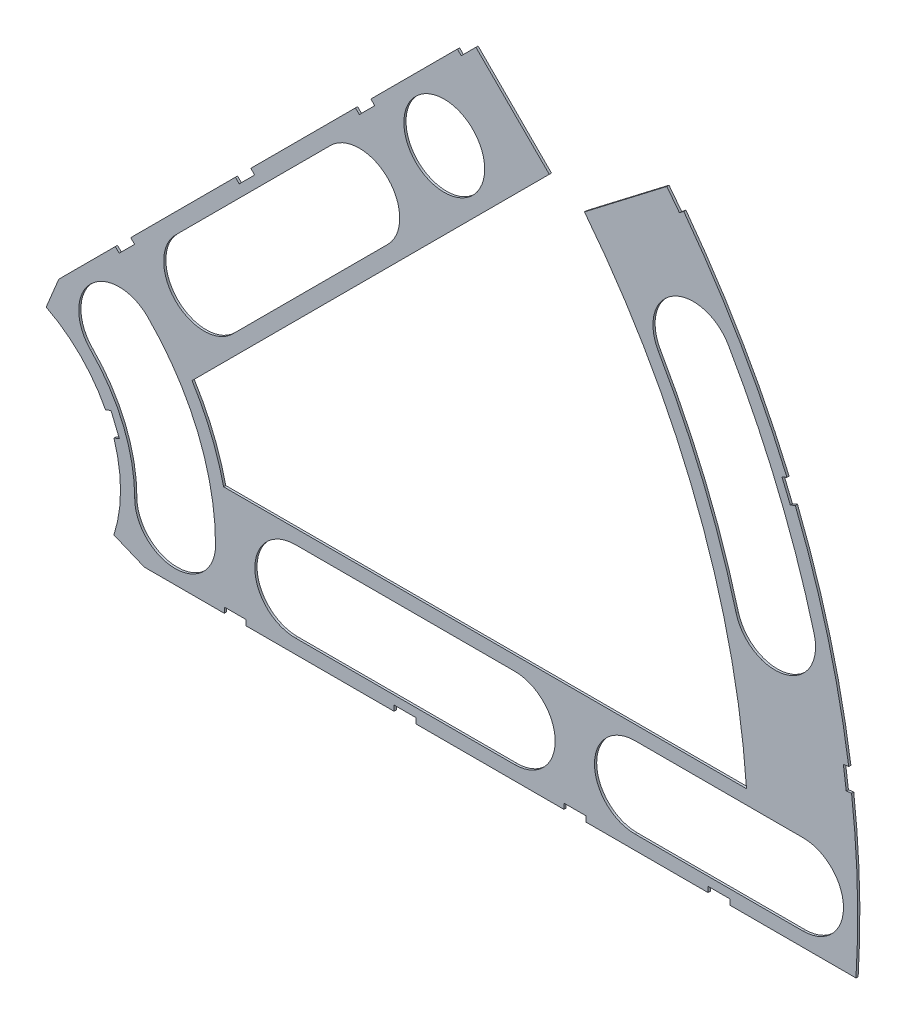
SolidWorks part; units mm, degrees
material "PTFE (general)"
ref_plane "Front Plane" through (0, 0, 0) normal (0, 0, 1) x (1, 0, 0)
ref_plane "Top Plane" through (0, 0, 0) normal (0, 1, 0) x (1, 0, 0)
ref_plane "Right Plane" through (0, 0, 0) normal (1, 0, 0) x (0, 0, -1)
sketch "Sketch1" plane through (0, 0, 0) normal (0, 0, 1) x (1, 0, 0)
  line L0 (0, 0) -> (320.3893, 0) construction
  line L1 (0, 0) -> (155.5285, 155.5285) construction
  line L2 (67.2115, 76.1917) -> (8.6967, 17.6769)
  line L3 (8.6967, 17.6769) -> (7.229, 14.1336)
  line L4 (101.4014, -6.35) -> (18.6489, -6.35)
  line L5 (15.1056, -4.8823) -> (18.6489, -6.35)
  line L6 (88.6729, 6.35) -> (27.8605, 6.35)
  line L9 (67.1914, 58.2111) -> (24.1905, 15.2102)
  line L10 (0, 0) -> (40.4486, 97.6516) construction
  line L11 (0, 0) -> (123.4567, -51.1374) construction
  line L18 (8.6967, 17.6769) -> (13.294, 8.6183) construction
  line L19 (18.6489, -6.35) -> (15.4943, 3.3063) construction
  line L20 (27.8605, 6.35) -> (27.7442, 6.7059) construction
  line L21 (24.1905, 15.2102) -> (24.3599, 14.8764) construction
  arc A0 (7.229, 14.1336) -> (15.1056, -4.8823) centre (0, 0) cw
  arc A1 (67.2115, 76.1917) -> (101.4014, -6.35) centre (0, 0) cw
  arc A2 (24.1905, 15.2102) -> (27.8605, 6.35) centre (0, 0) cw
  arc A3 (67.1914, 58.2111) -> (88.6729, 6.35) centre (0, 0) cw
  arc A8 (13.294, 8.6183) -> (15.4943, 3.3063) centre (0, 0) cw construction
  arc A9 (24.3599, 14.8764) -> (27.7442, 6.7059) centre (0, 0) cw construction
  dimension "D1" = 45
  dimension "D3" = 6.35
  dimension "D4" = 15.875
  dimension "D7" = 22.5
  dimension "D8" = 101.6
  dimension "D11" = 12.7
  dimension "D12" = 12.7
  dimension "D2" = 6.35
  dimension "D5" = 67.5
  dimension "D9" = 1.27
  dimension "D10" = 1.27
  dimension "D6" = 12.7
extrude "Boss-Extrude1" add sketch "Sketch1" along normal blind 0.254
sketch "Sketch2" plane through (0, 0, 0.254) normal (0, 0, 1) x (1, 0, 0)
  line L0 (0, 0) -> (101.6, 0) construction
  line L1 (0, 0) -> (71.842, 71.842) construction
  line L3 (0, 0) -> (22.225, 0) construction
  line L4 (0, 0) -> (15.7154, 15.7154) construction
  line L5 (0, 0) -> (95.25, 0) construction
  line L6 (0, 0) -> (92.0044, 24.6525) construction
  arc A0 (101.4014, -6.35) -> (67.2115, 76.1917) centre (0, 0) ccw construction
  circle A1 centre (22.225, 0) radius 4.699
  arc A2 (15.1056, -4.8823) -> (7.229, 14.1336) centre (0, 0) ccw construction
  circle A3 centre (36.195, 0) radius 4.699
  circle A4 centre (61.722, 0) radius 4.699
  circle A5 centre (75.692, 0) radius 4.699
  circle A6 centre (95.25, 0) radius 4.699
  circle A7 centre (15.7154, 15.7154) radius 4.699
  circle A8 centre (25.5937, 25.5937) radius 4.699
  circle A9 centre (43.644, 43.644) radius 4.699
  circle A10 centre (53.5223, 53.5223) radius 4.699
  circle A11 centre (92.0044, 24.6525) radius 4.699
  circle A12 centre (82.4889, 47.625) radius 4.699
  circle A13 centre (67.3519, 67.3519) radius 4.699
  dimension "D3" = 9.398
  dimension "D1" = 45
  dimension "D2" = 6.35
  dimension "D4" = 6.35
  dimension "D5" = 13.97
  dimension "D7" = 13.97
  dimension "D8" = 19.558
  dimension "D9" = 45
  dimension "D10" = 15
  dimension "D11" = 25.527
  dimension "D6" = 2
extrude "Cut-Extrude1" cut sketch "Sketch2" against normal through all
sketch "Sketch3" plane through (0, 0, 0.254) normal (0, 0, 1) x (1, 0, 0)
  line L0 (15.2664, 24.2467) -> (17.0625, 26.0427)
  line L1 (15.2664, 24.2467) -> (15.7154, 23.7977)
  line L2 (17.0625, 26.0427) -> (17.5115, 25.5937)
  line L3 (15.7154, 23.7977) -> (17.5115, 25.5937)
  line L4 (67.2115, 76.1917) -> (8.6967, 17.6769) construction
  line L5 (44.9911, 53.9713) -> (43.195, 52.1753)
  line L6 (44.9911, 53.9713) -> (45.4401, 53.5223)
  line L7 (43.195, 52.1753) -> (43.644, 51.7263)
  line L8 (45.4401, 53.5223) -> (43.644, 51.7263)
  line L9 (27.94, -6.35) -> (30.48, -6.35)
  line L10 (27.94, -6.35) -> (27.94, -5.715)
  line L11 (30.48, -6.35) -> (30.48, -5.715)
  line L12 (27.94, -5.715) -> (30.48, -5.715)
  line L13 (18.6489, -6.35) -> (101.4014, -6.35) construction
  line L14 (67.437, -6.35) -> (69.977, -6.35)
  line L15 (67.437, -6.35) -> (67.437, -5.715)
  line L16 (69.977, -6.35) -> (69.977, -5.715)
  line L17 (67.437, -5.715) -> (69.977, -5.715)
  line L18 (29.2307, 38.211) -> (31.0268, 40.007)
  line L19 (29.2307, 38.211) -> (29.6797, 37.762)
  line L20 (31.0268, 40.007) -> (31.4758, 39.558)
  line L21 (29.6797, 37.762) -> (31.4758, 39.558)
  line L22 (56.845, 65.8253) -> (55.049, 64.0292)
  line L23 (56.845, 65.8253) -> (57.294, 65.3763)
  line L24 (55.049, 64.0292) -> (55.498, 63.5802)
  line L25 (57.294, 65.3763) -> (55.498, 63.5802)
  line L26 (47.6885, -6.35) -> (50.2285, -6.35)
  line L27 (47.6885, -6.35) -> (47.6885, -5.715)
  line L28 (50.2285, -6.35) -> (50.2285, -5.715)
  line L29 (47.6885, -5.715) -> (50.2285, -5.715)
  line L30 (84.201, -6.35) -> (86.741, -6.35)
  line L31 (84.201, -6.35) -> (84.201, -5.715)
  line L32 (86.741, -6.35) -> (86.741, -5.715)
  line L33 (84.201, -5.715) -> (86.741, -5.715)
  line L34 (0, 0) -> (100.7308, 13.2615) construction
  line L35 (0, 0) -> (93.8662, 38.8806) construction
  line L36 (0, 0) -> (80.6047, 61.8502) construction
  line L37 (0, 0) -> (101.6, 0) construction
  line L38 (99.9355, 14.4377) -> (100.267, 11.9194)
  line L39 (99.9355, 14.4377) -> (101.1946, 14.6035)
  line L40 (100.267, 11.9194) -> (101.5261, 12.0852)
  line L41 (101.1946, 14.6035) -> (101.5261, 12.0852)
  line L42 (99.9355, 14.4377) -> (101.5261, 12.0852) construction
  line L43 (100.267, 11.9194) -> (101.1946, 14.6035) construction
  line L44 (93.7655, 37.4643) -> (94.9388, 37.9503)
  line L45 (93.7655, 37.4643) -> (92.7935, 39.811)
  line L46 (94.9388, 37.9503) -> (93.9668, 40.297)
  line L47 (92.7935, 39.811) -> (93.9668, 40.297)
  line L48 (93.7655, 37.4643) -> (93.9668, 40.297) construction
  line L49 (94.9388, 37.9503) -> (92.7935, 39.811) construction
  line L50 (79.3278, 62.4712) -> (80.874, 60.456)
  line L51 (79.3278, 62.4712) -> (80.3354, 63.2443)
  line L52 (80.874, 60.456) -> (81.8816, 61.2292)
  line L53 (80.3354, 63.2443) -> (81.8816, 61.2292)
  line L54 (79.3278, 62.4712) -> (81.8816, 61.2292) construction
  line L55 (80.874, 60.456) -> (80.3354, 63.2443) construction
  line L56 (13.5939, 7.0054) -> (14.5659, 4.6588)
  line L57 (13.5939, 7.0054) -> (14.7672, 7.4914)
  line L58 (14.5659, 4.6588) -> (15.7393, 5.1448)
  line L59 (14.7672, 7.4914) -> (15.7393, 5.1448)
  line L60 (13.5939, 7.0054) -> (15.7393, 5.1448) construction
  line L61 (14.5659, 4.6588) -> (14.7672, 7.4914) construction
  circle A0 centre (15.7154, 15.7154) radius 4.699 construction
  circle A1 centre (43.644, 43.644) radius 4.699 construction
  circle A2 centre (22.225, 0) radius 4.699 construction
  circle A3 centre (61.722, 0) radius 4.699 construction
  arc A4 (101.4014, -6.35) -> (67.2115, 76.1917) centre (0, 0) ccw construction
  arc A9 (15.1056, -4.8823) -> (7.229, 14.1336) centre (0, 0) ccw construction
  circle A10 centre (36.195, 0) radius 4.699 construction
  circle A11 centre (75.692, 0) radius 4.699 construction
  circle A12 centre (25.5937, 25.5937) radius 4.699 construction
  circle A13 centre (53.5223, 53.5223) radius 4.699 construction
  point P75 (14.6666, 6.0751)
  dimension "D2" = 5.715
  dimension "D3" = 2.54
  dimension "D6" = 5.715
  dimension "D8" = 0.635
  dimension "D9" = 5.715
  dimension "D12" = 5.715
  dimension "D4" = 7.5
  dimension "D5" = 22.5
  dimension "D7" = 37.5
  dimension "D10" = 90
  dimension "D11" = 1.27
  dimension "D14" = 0.635
  dimension "D15" = 90
  dimension "D18" = 0.635
  dimension "D19" = 90
  dimension "D22" = 0.635
  dimension "D20" = 1.27
  dimension "D17" = 0.635
  dimension "D13" = 11.4935
  dimension "D16" = 8.509
  dimension "D21" = 11.4935
  dimension "D23" = 8.509
extrude "Cut-Extrude2" cut sketch "Sketch3" against normal through all
sketch "Sketch5" plane through (0, 0, 0.254) normal (0, 0, 1) x (1, 0, 0)
  line L0 (0, 0) -> (85.5465, 65.6421) construction
  line L1 (55.8572, 66.6335) -> (68.4933, 53.9974)
  line L2 (68.4933, 53.9974) -> (81.5013, 63.9789)
  line L3 (67.3519, 78.1282) -> (81.5013, 63.9789)
  line L5 (67.3519, 78.1282) -> (55.8572, 66.6335)
  line L8 (69.977, -6.35) -> (84.201, -6.35) construction
  line L9 (55.049, 64.0292) -> (55.498, 63.5802) construction
  line L10 (67.2115, 76.1917) -> (56.845, 65.8253) construction
  arc A1 (79.8253, 62.8529) -> (67.2115, 76.1917) centre (0, 0) ccw construction
  dimension "D3" = 1.27
  dimension "D1" = 37.5
  dimension "D2" = 2.413
  dimension "D4" = 1.27
  dimension "D5" = 1.143
sketch "Sketch6" plane through (0, 0, 0.254) normal (0, 0, 1) x (1, 0, 0)
  line L0 (0, 0) -> (101.6, 0) construction
  line L1 (0, 0) -> (71.842, 71.842) construction
  line L2 (0, 0) -> (87.9882, 50.8) construction
  line L3 (0, 0) -> (98.1381, 26.296) construction
  line L4 (25.5937, 25.5937) -> (43.644, 43.644) construction
  line L5 (22.271, 28.9164) -> (40.3213, 46.9667)
  line L6 (28.9164, 22.271) -> (46.9667, 40.3213)
  line L10 (61.722, 0) -> (36.195, 0) construction
  line L11 (61.722, -4.699) -> (36.195, -4.699)
  line L12 (61.722, 4.699) -> (36.195, 4.699)
  line L13 (95.25, 0) -> (75.692, 0) construction
  line L14 (95.25, -4.699) -> (75.692, -4.699)
  line L15 (95.25, 4.699) -> (75.692, 4.699)
  arc A0 (79.8253, 62.8529) -> (67.2115, 76.1917) centre (0, 0) ccw construction
  arc A1 (15.7154, 15.7154) -> (22.225, 0) centre (0, 0) cw construction
  arc A2 (26.924, 0) -> (19.0381, 19.0381) centre (0, 0) ccw
  arc A3 (17.526, 0) -> (12.3928, 12.3928) centre (0, 0) ccw
  arc A4 (17.526, 0) -> (26.924, 0) centre (22.225, 0) ccw
  arc A5 (101.4014, -6.35) -> (100.8887, 12.0013) centre (0, 0) ccw construction
  arc A6 (19.0381, 19.0381) -> (12.3928, 12.3928) centre (15.7154, 15.7154) ccw
  arc A7 (93.3728, 40.0509) -> (81.3715, 60.8378) centre (0, 0) ccw construction
  arc A8 (100.5572, 14.5196) -> (94.3448, 37.7043) centre (0, 0) ccw construction
  arc A9 (82.4889, 47.625) -> (92.0044, 24.6525) centre (0, 0) cw construction
  arc A10 (96.5433, 25.8687) -> (86.5584, 49.9745) centre (0, 0) ccw
  arc A11 (87.4655, 23.4363) -> (78.4195, 45.2755) centre (0, 0) ccw
  arc A12 (87.4655, 23.4363) -> (96.5433, 25.8687) centre (92.0044, 24.6525) ccw
  arc A13 (86.5584, 49.9745) -> (78.4195, 45.2755) centre (82.4889, 47.625) ccw
  arc A14 (22.271, 28.9164) -> (28.9164, 22.271) centre (25.5937, 25.5937) ccw
  arc A15 (46.9667, 40.3213) -> (40.3213, 46.9667) centre (43.644, 43.644) ccw
  circle A16 centre (43.644, 43.644) radius 4.699 construction
  arc A18 (61.722, -4.699) -> (61.722, 4.699) centre (61.722, 0) ccw
  arc A19 (36.195, 4.699) -> (36.195, -4.699) centre (36.195, 0) ccw
  arc A20 (95.25, -4.699) -> (95.25, 4.699) centre (95.25, 0) ccw
  arc A21 (75.692, 4.699) -> (75.692, -4.699) centre (75.692, 0) ccw
  point P8 (20.5332, 8.5051)
  point P12 (87.9995, 36.4506)
  point P43 (34.6189, 34.6189)
  point P59 (48.9585, 0)
  point P70 (85.471, 0)
  dimension "D2" = 9.398
  dimension "D5" = 9.398
  dimension "D1" = 45
  dimension "D3" = 9.398
  dimension "D4" = 9.398
extrude "Cut-Extrude4" cut sketch "Sketch6" against normal through all
extrude "Cut-Extrude5" cut sketch "Sketch5" against normal through all
equation "\"cSep\"= 1.005"
equation "\"D11@Sketch2\"=\"cSep\""
equation "\"cSep2\"= \"D8@Sketch2\""
equation "\"D13@Sketch3\"=\"cSep\"/2-.05"
equation "\"D16@Sketch3\"=\"cSep2\"/2-.05"
equation "\"D21@Sketch3\"=\"cSep\"/2-.05"
equation "\"D23@Sketch3\"=\"cSep2\"/2-.05"
